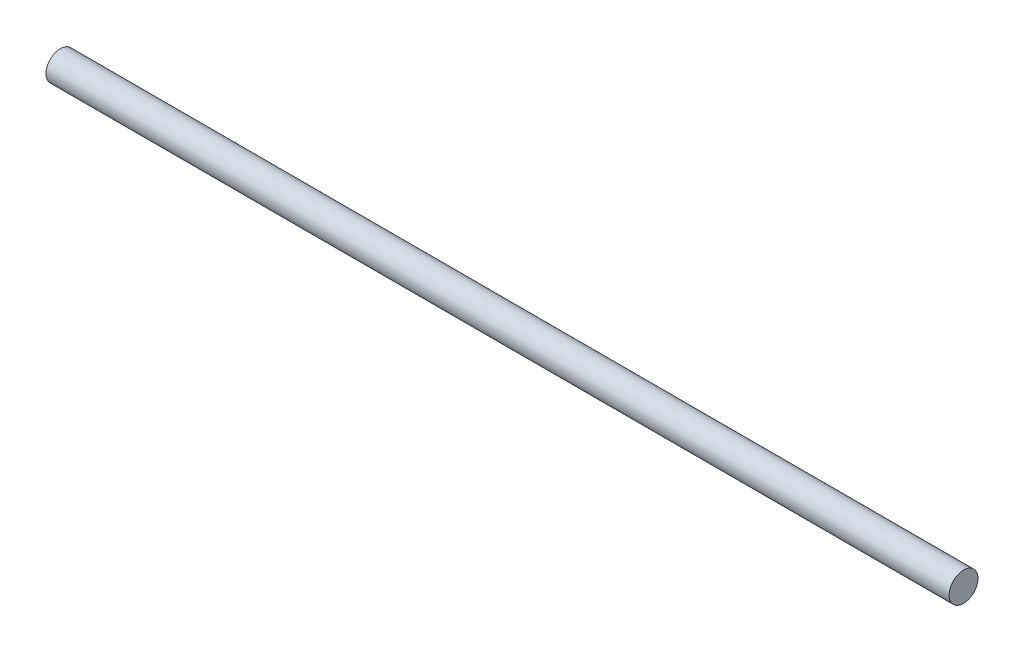
SolidWorks part; units mm, degrees
ref_plane "Front Plane" through (0, 0, 0) normal (0, 0, 1) x (1, 0, 0)
ref_plane "Top Plane" through (0, 0, 0) normal (0, 1, 0) x (1, 0, 0)
ref_plane "Right Plane" through (0, 0, 0) normal (1, 0, 0) x (0, 0, -1)
sketch "Sketch2" plane through (0, 0, 0) normal (1, 0, 0) x (0, 0, -1)
  circle A0 centre (0, 0) radius 4
extrude "Boss-Extrude1" add sketch "Sketch2" along normal blind 250 contours A0
